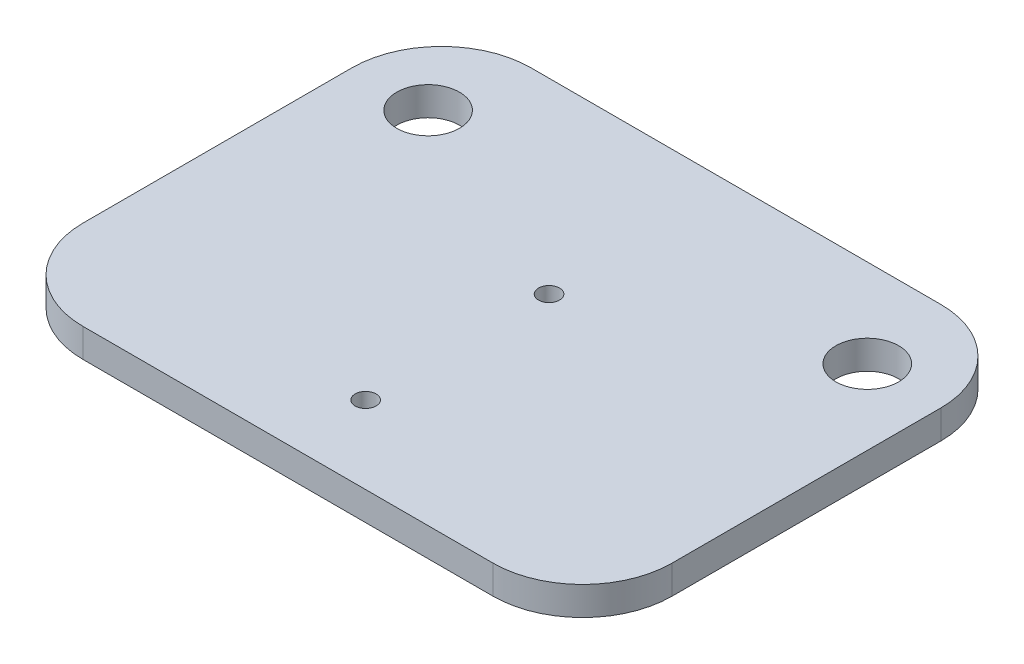
SolidWorks part; units mm, degrees
material "Custom Plastic"
ref_plane "Front Plane" through (0, 0, 0) normal (0, 0, 1) x (1, 0, 0)
ref_plane "Top Plane" through (0, 0, 0) normal (0, 1, 0) x (1, 0, 0)
ref_plane "Right Plane" through (0, 0, 0) normal (1, 0, 0) x (0, 0, -1)
sketch "Sketch1" plane through (0, 0, 0) normal (0, 1, 0) x (1, 0, 0)
  line L1 (-5.81, -6.35) -> (5.81, -6.35)
  line L2 (-8.35, -3.81) -> (-8.35, 3.81)
  line L3 (-5.81, 6.35) -> (5.81, 6.35)
  line L4 (8.35, -3.81) -> (8.35, 3.81)
  line L5 (-8.35, -6.35) -> (8.35, 6.35) construction
  line L6 (-8.35, 6.35) -> (8.35, -6.35) construction
  arc A0 (-8.35, -3.81) -> (-5.81, -6.35) centre (-5.81, -3.81) ccw
  arc A1 (5.81, -6.35) -> (8.35, -3.81) centre (5.81, -3.81) ccw
  arc A2 (8.35, 3.81) -> (5.81, 6.35) centre (5.81, 3.81) ccw
  arc A3 (-5.81, 6.35) -> (-8.35, 3.81) centre (-5.81, 3.81) ccw
  point P0 (0, 0)
  dimension "D3" = 2.54
  dimension "D1" = 16.7
  dimension "D2" = 12.7
extrude "Boss-Extrude1" add sketch "Sketch1" along normal blind 0.8128
ref_plane "PlaneforHoles" through (0, 2.54, 0) normal (0, 1, 0) x (1, 0, 0)
sketch "Sketch2" plane through (0, 2.54, 0) normal (0, 1, 0) x (1, 0, 0)
  line L0 (-11.8989, 3.85) -> (12.7354, 3.85) construction
  line L1 (0, -10.8525) -> (0, 10.6929) construction
  line L2 (-11.7813, -4.15) -> (12.6218, -4.15) construction
  line L3 (5.81, 6.35) -> (-5.81, 6.35) construction
  line L4 (11.7813, 1.05) -> (-11.7813, 1.05) construction
  line L5 (-5.81, -6.35) -> (5.81, -6.35) construction
  circle A1 centre (0, 3.85) radius 6.223 construction
  circle A3 centre (-6.2284, 3.85) radius 0.889
  circle A4 centre (6.223, 3.85) radius 0.889
  circle A5 centre (0, -4.15) radius 0.2972
  circle A6 centre (0, 1.05) radius 0.2972
  point P19 (0, 1.05)
  dimension "D1" = 2.5
  dimension "D2" = 7.4
  dimension "D3" = 2.2
extrude "Cut-Extrude1" cut sketch "Sketch2" against normal blind 8.4328
